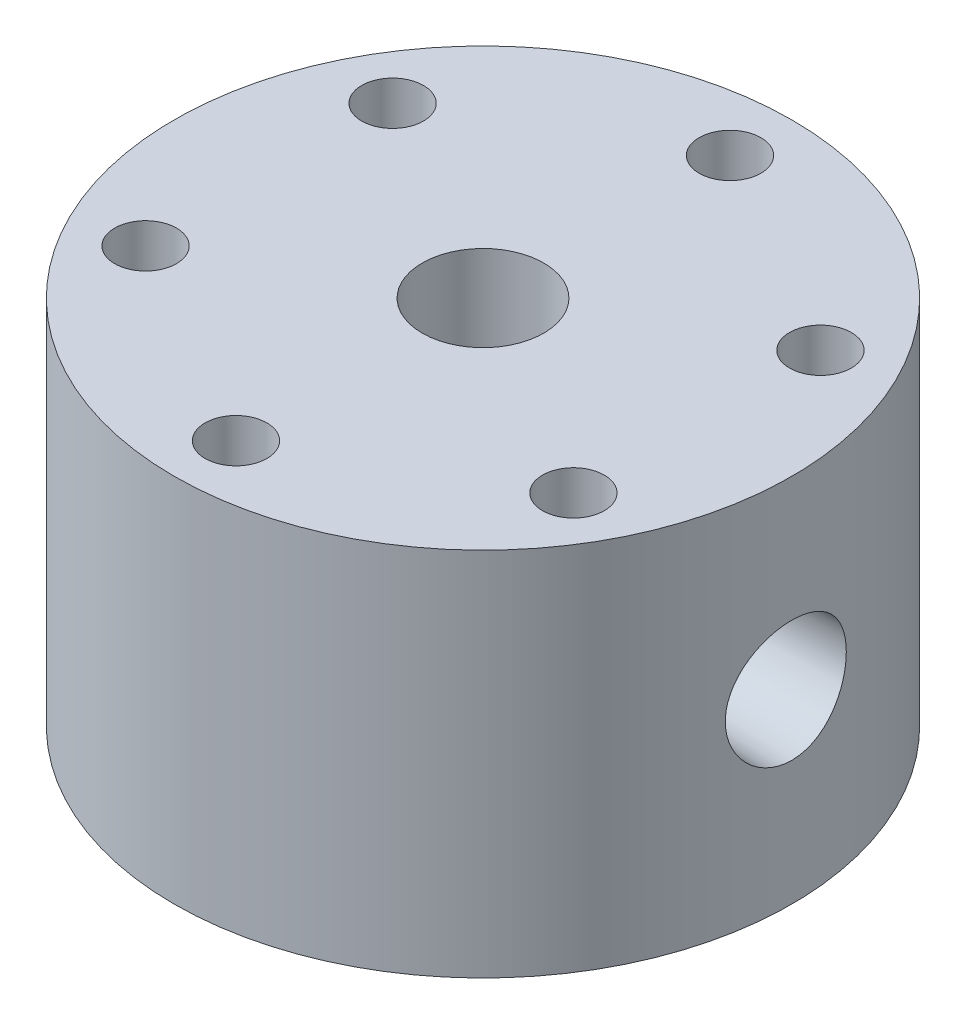
SolidWorks part; units mm, degrees
ref_plane "Front Plane" through (0, 0, 0) normal (0, 0, 1) x (1, 0, 0)
ref_plane "Top Plane" through (0, 0, 0) normal (0, 1, 0) x (1, 0, 0)
ref_plane "Right Plane" through (0, 0, 0) normal (1, 0, 0) x (0, 0, -1)
sketch "Sketch1" plane through (0, 0, 0) normal (0, 0, 1) x (1, 0, 0)
  line L2 (-12.7, 0) -> (-31.75, 0)
  line L3 (-31.75, 0) -> (-31.75, 38.1)
  line L4 (-31.75, 38.1) -> (-3.81, 38.1)
  line L6 (-3.81, 38.1) -> (-3.81, 6.35)
  line L10 (0, 0) -> (0, 15.7692) construction
  line L11 (-11.1125, 6.35) -> (-12.7, 6.35)
  line L12 (-12.7, 6.35) -> (-12.7, 0)
  line L13 (-3.81, 6.35) -> (-8.0645, 6.35)
  line L14 (-8.0645, 6.35) -> (-8.0645, 8.382)
  line L15 (-8.0645, 8.382) -> (-11.1125, 8.382)
  line L16 (-11.1125, 8.382) -> (-11.1125, 6.35)
  point P2 (-12.457, 0)
  dimension "D1" = 3.81
  dimension "D2" = 12.7
  dimension "D3" = 6.35
  dimension "D4" = 38.1
  dimension "D5" = 31.75
  dimension "D6" = 3.048
  dimension "D7" = 2.032
  dimension "D8" = 1.5875
revolve "Revolve1" add sketch "Sketch1" angle 360 about L10
hole_wizard "M14x1.5 Tapped Hole1" positions "Sketch2" profile "Sketch4" tap size "M14x1.5" standard "ANSI Metric"
sketch "Sketch2" plane through (0, 38.1, 0) normal (0, 1, 0) x (1, 0, 0)
  point P0 (0, 0)
sketch "Sketch4" plane through (0, 38.1, 0) normal (1, 0, 0) x (0, 0, 1)
  line L0 (0, 0) -> (0, 29.1554)
  line L1 (0, 29.1554) -> (6.25, 25.4)
  line L2 (6.25, 25.4) -> (6.25, 0)
  line L5 (6.25, 0) -> (0, 0)
  line L10 (0, 29.1554) -> (-6.25, 25.4) construction
  line L11 (0, -6.35) -> (0, 107.95) construction
  dimension "Tap Drill Dia." = 12.5
  dimension "Tap Drill Depth" = 25.4
  dimension "Drill Angle" = 118
cosmetic thread "Hole Thread3" parameters "D1"=27.94, "D2"=14
ref_plane "Plane1" through (31.75, 0, 0) normal (1, 0, 0) x (0, 0, -1)
ref_plane "Plane2" through (-31.75, 0, 0) normal (-1, 0, 0) x (0, 0, 1)
hole_wizard "1/4 NPT Tapped Hole1" positions "Sketch5" profile "Sketch6" size "1/4" standard "ANSI Inch"
sketch "Sketch5" plane through (31.75, 0, 0) normal (1, 0, 0) x (0, 0, -1)
  line L0 (31.75, 38.1) -> (-31.75, 38.1) construction
  point P0 (0, 19.05)
  dimension "D1" = 19.05
sketch "Sketch6" plane through (31.75, 19.05, 0) normal (0, 1, 0) x (0, 0, -1)
  line L0 (0, 0) -> (0, 20.3603)
  line L1 (5.5626, 17.018) -> (0, 20.3603)
  line L2 (-5.5626, 17.018) -> (0, 20.3603) construction
  line L3 (5.5626, 17.018) -> (5.5626, 9.906)
  line L4 (5.5626, 9.906) -> (5.9437, 9.906)
  line L5 (5.9437, 9.906) -> (6.2403, 0)
  line L6 (-5.9437, 9.906) -> (-6.2403, 0) construction
  line L7 (6.2403, 0) -> (0, 0)
  line L8 (0, -6.35) -> (0, 107.95) construction
  line L11 (-5.5626, 9.906) -> (-5.9437, 9.906) construction
  dimension "Tap Drill Dia." = 11.1252
  dimension "Tap Drill Depth" = 17.018
  dimension "Thread Dia." = 12.4806
  dimension "Thread Angle" = 3.43
  dimension "Thread Depth" = 9.906
  dimension "Drill Angle" = 118
cosmetic thread "Hole Thread1" parameters "D1"=9.906, "D2"=13.7086
hole_wizard "1/4 NPT Tapped Hole2" positions "Sketch7" profile "Sketch8" size "1/4" standard "ANSI Inch"
sketch "Sketch7" plane through (-31.75, 0, 0) normal (-1, 0, 0) x (0, 0, 1)
  line L0 (31.75, 38.1) -> (-31.75, 38.1) construction
  point P0 (0, 19.05)
  dimension "D1" = 19.05
sketch "Sketch8" plane through (-31.75, 19.05, 0) normal (0, 1, 0) x (0, 0, 1)
  line L0 (0, 0) -> (0, 20.3603)
  line L1 (5.5626, 17.018) -> (0, 20.3603)
  line L2 (-5.5626, 17.018) -> (0, 20.3603) construction
  line L3 (5.5626, 17.018) -> (5.5626, 9.906)
  line L4 (5.5626, 9.906) -> (5.9437, 9.906)
  line L5 (5.9437, 9.906) -> (6.2403, 0)
  line L6 (-5.9437, 9.906) -> (-6.2403, 0) construction
  line L7 (6.2403, 0) -> (0, 0)
  line L8 (0, -6.35) -> (0, 107.95) construction
  line L11 (-5.5626, 9.906) -> (-5.9437, 9.906) construction
  dimension "Tap Drill Dia." = 11.1252
  dimension "Tap Drill Depth" = 17.018
  dimension "Thread Dia." = 12.4806
  dimension "Thread Angle" = 3.43
  dimension "Thread Depth" = 9.906
  dimension "Drill Angle" = 118
cosmetic thread "Hole Thread2" parameters "D1"=9.906, "D2"=13.7086
hole_wizard "1/16 (0.0625) Diameter Hole1" positions "Sketch9" profile "Sketch10" hole size "1/16" standard "ANSI Inch"
sketch "Sketch9" plane through (31.75, 0, 0) normal (1, 0, 0) x (0, 0, -1)
  point P0 (0, 19.05)
sketch "Sketch10" plane through (31.75, 19.05, 0) normal (0, 1, 0) x (0, 0, -1)
  line L0 (0, 0) -> (0, 29.0519)
  line L1 (0, 29.0519) -> (0.7937, 28.575)
  line L2 (0.7937, 28.575) -> (0.7937, 0)
  line L5 (0.7937, 0) -> (0, 0)
  line L10 (0, 29.0519) -> (-0.7938, 28.575) construction
  line L11 (0, -6.35) -> (0, 107.95) construction
  dimension "Hole Dia." = 1.5875
  dimension "Hole Depth" = 28.575
  dimension "Drill Angle" = 118
hole_wizard "3/32 (0.09375) Diameter Hole1" positions "Sketch11" profile "Sketch12" hole size "3/32" standard "ANSI Inch"
sketch "Sketch11" plane through (-31.75, 0, 0) normal (-1, 0, 0) x (0, 0, 1)
  point P0 (0, 19.05)
sketch "Sketch12" plane through (-31.75, 19.05, 0) normal (0, 1, 0) x (0, 0, 1)
  line L0 (0, 0) -> (0, 29.4174)
  line L1 (0, 29.4174) -> (1.1906, 28.702)
  line L2 (1.1906, 28.702) -> (1.1906, 0)
  line L5 (1.1906, 0) -> (0, 0)
  line L10 (0, 29.4174) -> (-1.1906, 28.702) construction
  line L11 (0, -6.35) -> (0, 107.95) construction
  dimension "Hole Dia." = 2.3812
  dimension "Hole Depth" = 28.702
  dimension "Drill Angle" = 118
hole_wizard "1/4 (0.25) Diameter Hole1" positions "Sketch15" profile "Sketch16" hole size "1/4" standard "ANSI Inch" end condition through all
sketch "Sketch15" plane through (0, 38.1, 0) normal (0, 1, 0) x (1, 0, 0)
  line L0 (0, 0) -> (16.0984, 0) construction
  line L2 (0, 0) -> (21.997, 12.7) construction
  point P0 (21.997, 12.7)
  dimension "D1" = 25.4
  dimension "D2" = 30
sketch "Sketch16" plane through (21.997, 38.1, -12.7) normal (1, 0, 0) x (0, 0, 1)
  line L0 (0, 0) -> (0, 38.1)
  line L1 (0, 38.1) -> (3.175, 38.1)
  line L2 (3.175, 38.1) -> (3.175, 0)
  line L5 (3.175, 0) -> (0, 0)
  line L11 (0, -6.35) -> (0, 107.95) construction
  dimension "Thru Hole Dia." = 6.35
  dimension "Thru Hole Depth" = 38.1
pattern_circular "CirPattern1" count 6 over 360 about axis through (0, 0, 0) along (0, 1, 0) of "1/4 (0.25) Diameter Hole1"
ref_plane "Plane3" through (15.875, 0, -27.4963) normal (0.5, 0, -0.866) x (0, -1, 0)
hole_wizard "1/4 NPT Tapped Hole3" positions "Sketch17" profile "Sketch18" size "1/4" standard "ANSI Inch"
sketch "Sketch17" plane through (15.875, 0, -27.4963) normal (0.5, 0, -0.866) x (0, -1, 0)
  point P0 (-19.05, 0)
  point P3 (-19.05, 0)
  dimension "D1" = 19.05
sketch "Sketch18" plane through (15.875, 19.05, -27.4963) normal (0, 1, 0) x (-0.866, 0, -0.5)
  line L0 (0, 0) -> (0, 20.3603)
  line L1 (5.5626, 17.018) -> (0, 20.3603)
  line L2 (-5.5626, 17.018) -> (0, 20.3603) construction
  line L3 (5.5626, 17.018) -> (5.5626, 9.906)
  line L4 (5.5626, 9.906) -> (5.9437, 9.906)
  line L5 (5.9437, 9.906) -> (6.2403, 0)
  line L6 (-5.9437, 9.906) -> (-6.2403, 0) construction
  line L7 (6.2403, 0) -> (0, 0)
  line L8 (0, -6.35) -> (0, 107.95) construction
  line L11 (-5.5626, 9.906) -> (-5.9437, 9.906) construction
  dimension "Tap Drill Dia." = 11.1252
  dimension "Tap Drill Depth" = 17.018
  dimension "Thread Dia." = 12.4806
  dimension "Thread Angle" = 3.43
  dimension "Thread Depth" = 9.906
  dimension "Drill Angle" = 118
cosmetic thread "Hole Thread5" parameters "D1"=9.906, "D2"=13.7086
hole_wizard "1/32 (0.03125) Diameter Hole1" positions "Sketch21" profile "Sketch22" hole size "1/32" standard "ANSI Inch"
sketch "Sketch21" plane through (15.875, 0, -27.4963) normal (0.5, 0, -0.866) x (0, -1, 0)
  point P0 (-19.05, 0)
sketch "Sketch22" plane through (15.875, 19.05, -27.4963) normal (0, 1, 0) x (-0.866, 0, -0.5)
  line L0 (0, 0) -> (0, 28.8135)
  line L1 (0, 28.8135) -> (0.3969, 28.575)
  line L2 (0.3969, 28.575) -> (0.3969, 0)
  line L5 (0.3969, 0) -> (0, 0)
  line L10 (0, 28.8135) -> (-0.3969, 28.575) construction
  line L11 (0, -6.35) -> (0, 107.95) construction
  dimension "Hole Dia." = 0.7937
  dimension "Hole Depth" = 28.575
  dimension "Drill Angle" = 118
